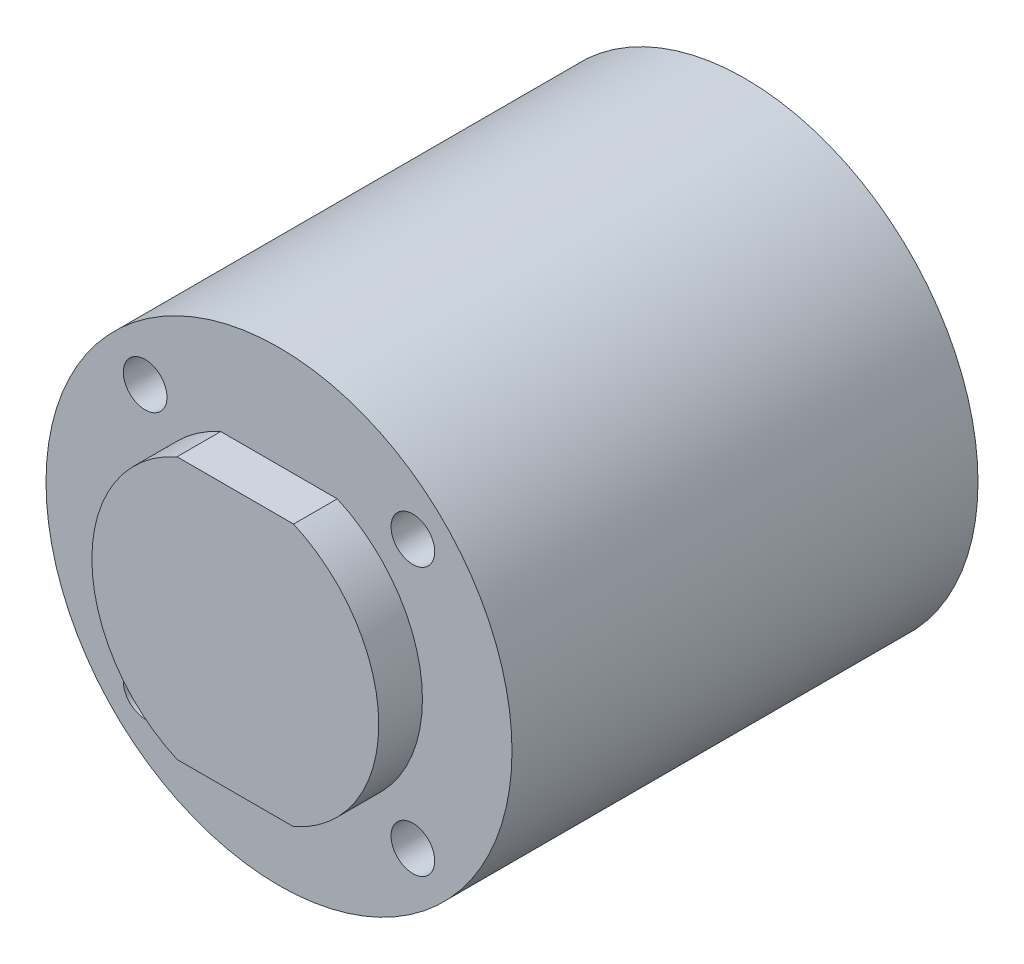
SolidWorks part; units mm, degrees
ref_plane "Front Plane" through (0, 0, 0) normal (0, 0, 1) x (1, 0, 0)
ref_plane "Top Plane" through (0, 0, 0) normal (0, 1, 0) x (1, 0, 0)
ref_plane "Right Plane" through (0, 0, 0) normal (1, 0, 0) x (0, 0, -1)
sketch "Sketch1" plane through (0, 0, 0) normal (0, 0, 1) x (1, 0, 0)
  line L0 (0, 0) -> (0, 9) construction
  line L1 (-4.0028, 9) -> (4.0028, 9)
  line L2 (-9.85, 0) -> (9.85, 0) construction
  line L3 (-4.0028, -9) -> (4.0028, -9)
  arc A0 (-4.0028, 9) -> (-4.0028, -9) centre (0, 0) ccw
  arc A1 (4.0028, -9) -> (4.0028, 9) centre (0, 0) ccw
  point P7 (0, 9)
  point P10 (0, 0)
  dimension "D1" = 19.7
  dimension "D2" = 9
extrude "Boss-Extrude1" add sketch "Sketch1" along normal blind 3
sketch "Sketch2" plane through (0, 0, 0) normal (0, 0, -1) x (-1, 0, 0)
  circle A0 centre (0, 0) radius 16
  dimension "D1" = 32
extrude "Boss-Extrude2" add sketch "Sketch2" along normal blind 32
sketch "Sketch5" plane through (0, 0, 3) normal (0, 0, 1) x (1, 0, 0)
  circle A0 centre (0, 0) radius 3
  dimension "D1" = 6
sketch "Sketch6" plane through (0, 0, 0) normal (0, 0, 1) x (1, 0, 0)
  line L0 (-13, 0) -> (13, 0) construction
  line L1 (0, 0) -> (-9.1924, 9.1924) construction
  circle A0 centre (0, 0) radius 13 construction
  circle A1 centre (-9.1924, 9.1924) radius 1.5
  circle A2 centre (9.1924, 9.1924) radius 1.5
  circle A3 centre (9.1924, -9.1924) radius 1.5
  circle A4 centre (-9.1924, -9.1924) radius 1.5
  point P16 (0, 0)
  dimension "D1" = 26
  dimension "D3" = 3
  dimension "D2" = 45
  dimension "D4" = 4
extrude "Cut-Extrude1" cut sketch "Sketch6" against normal blind 10 contours A2 | A1 | A4 | A3
